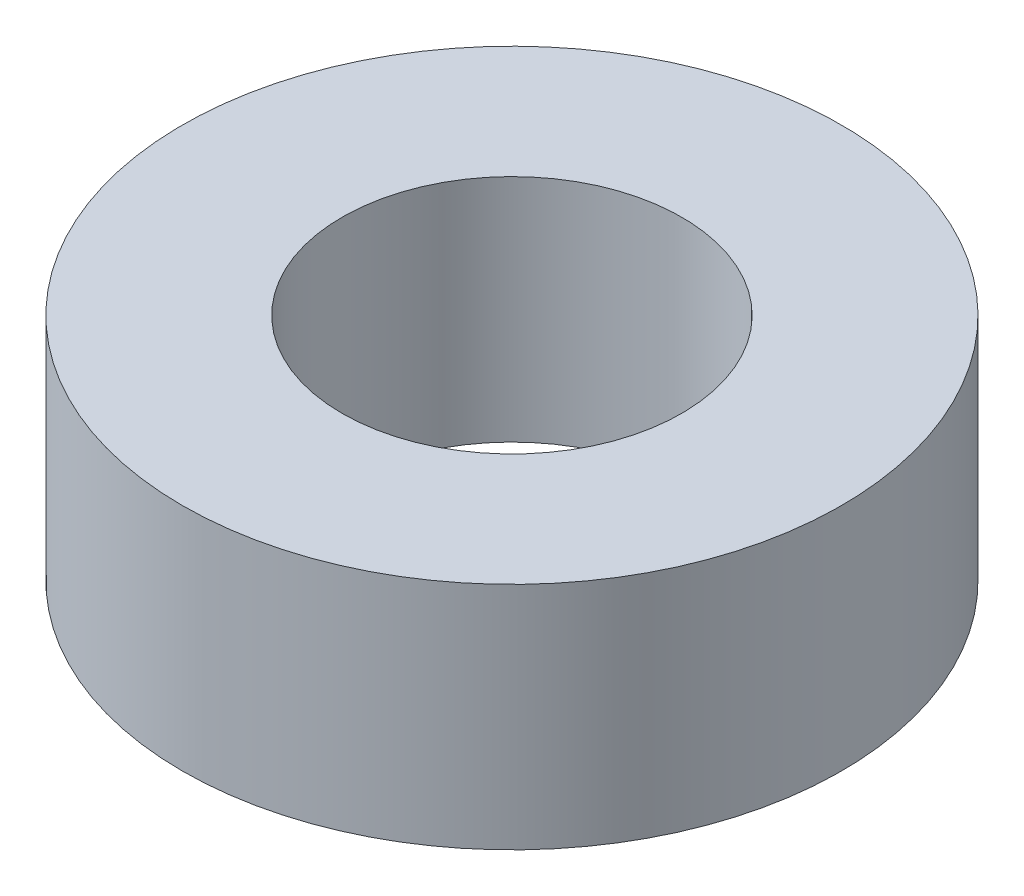
SolidWorks part; units mm, degrees
material "PET"
ref_plane "Front" through (0, 0, 0) normal (0, 0, 1) x (1, 0, 0)
ref_plane "Top" through (0, 0, 0) normal (0, 1, 0) x (1, 0, 0)
ref_plane "Right" through (0, 0, 0) normal (1, 0, 0) x (0, 0, -1)
sketch "Sketch1" plane through (0, 0, 0) normal (0, 1, 0) x (1, 0, 0)
  circle A0 centre (0, 0) radius 3.3782
  circle A1 centre (0, 0) radius 6.5532
  dimension "D1" = 6.7564
  dimension "D2" = 3.175
extrude "Boss-Extrude1" add sketch "Sketch1" along normal blind 4.572
